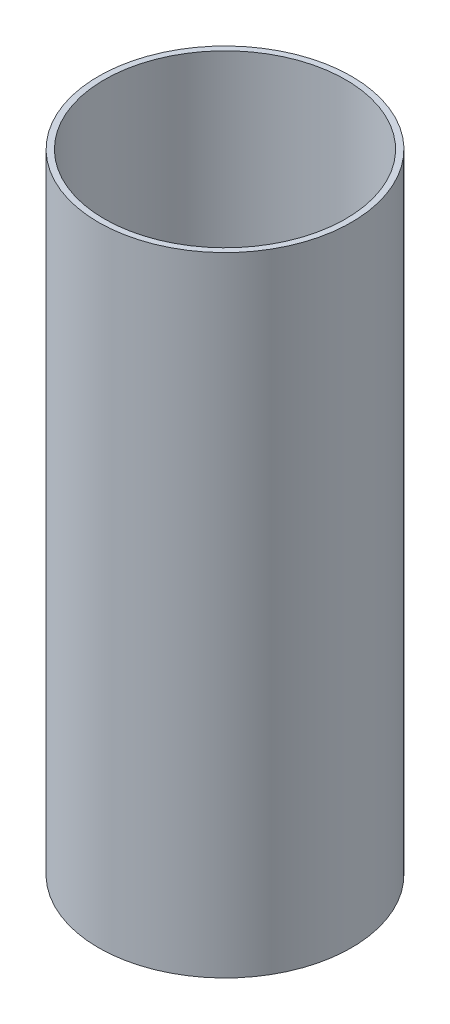
SolidWorks part; units mm, degrees
ref_plane "Front Plane" through (0, 0, 0) normal (0, 0, 1) x (1, 0, 0)
ref_plane "Top Plane" through (0, 0, 0) normal (0, 1, 0) x (1, 0, 0)
ref_plane "Right Plane" through (0, 0, 0) normal (1, 0, 0) x (0, 0, -1)
sketch "Sketch1" plane through (0, 0, 0) normal (0, 1, 0) x (1, 0, 0)
  circle A0 centre (0, 0) radius 57.15
  circle A1 centre (0, 0) radius 59.94
  dimension "D1" = 114.3
  dimension "D2" = 2.79
extrude "Boss-Extrude1" add sketch "Sketch1" along normal blind 297.6
